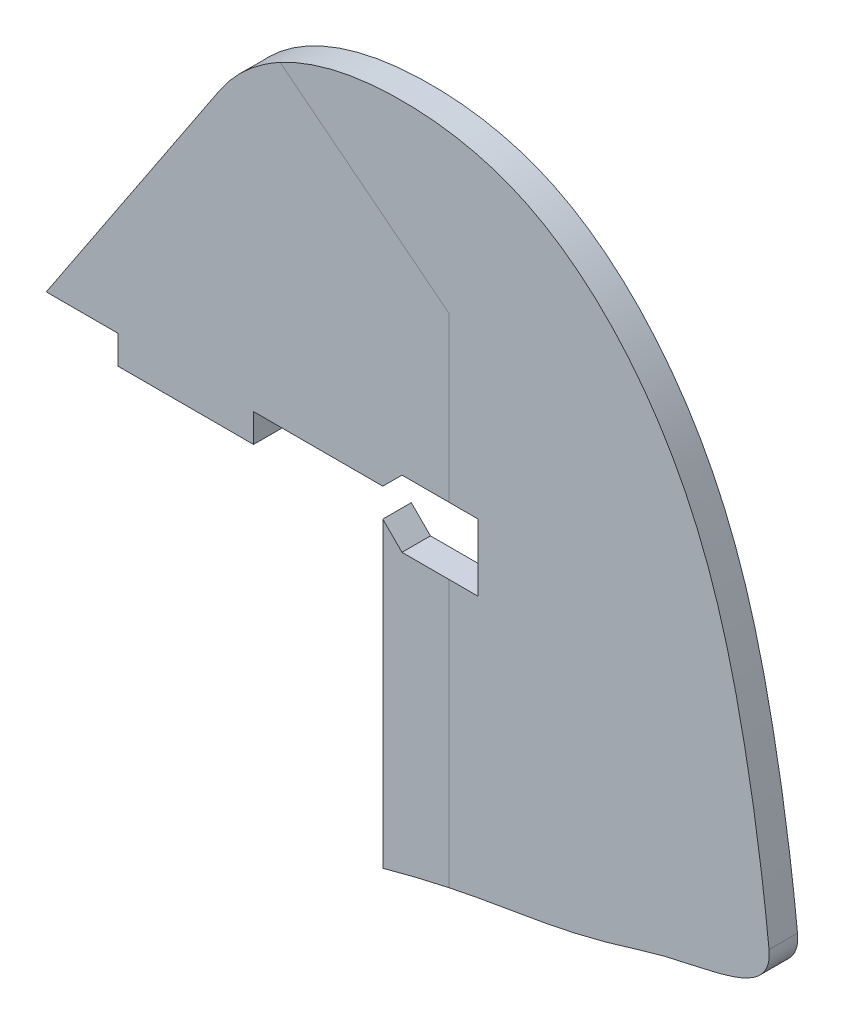
SolidWorks part; units mm, degrees
ref_plane "Front" through (0, 0, 0) normal (0, 0, 1) x (1, 0, 0)
ref_plane "Top" through (0, 0, 0) normal (0, 1, 0) x (1, 0, 0)
ref_plane "Right" through (0, 0, 0) normal (1, 0, 0) x (0, 0, -1)
sketch "Sketch1" plane through (0, 0, 0) normal (0, 0, 1) x (1, 0, 0)
  line L0 (-609.9474, 216.5894) -> (1528.7193, 216.5894) construction
  line L1 (2.6601, 4.007) -> (35.1257, 52.9107)
  line L2 (65.6661, 0) -> (65.6661, 4.007)
  line L3 (65.6661, 4.007) -> (2.6601, 4.007)
  line L4 (65.6661, -57.9378) -> (65.6661, 0)
  line L5 (65.6661, 0) -> (0, 0) construction
  line L6 (78.0167, 38.2576) -> (46.4421, 63.112)
  line L7 (78.0167, 38.2576) -> (78.0167, -55.0278)
  spline S0 degree 3 poles (35.1257, 52.9107) (37.9474, 57.1612) (47.9711, 65.9423) (69.0084, 69.7517) (98.5076, 64.2412) (123.1022, 36.6886) (133.3175, 0.0651) (136.8079, -23.843) (137.976, -34.9736) knots 0 0 0 0 0.083245 0.226859 0.347289 0.588091 0.805835 1 1 1 1
  spline S1 degree 3 poles (137.976, -34.9736) (138.8152, -42.9691) (124.6399, -43.6095) (103.2327, -50.58) (88.628, -52.8063) (74.994, -55.3617) (65.6661, -57.9378) knots 0 0 0 0 0.302584 0.37189 0.693053 1 1 1 1
extrude "Boss-Extrude1" add sketch "Sketch1" along normal mid plane 5.334
split line "Split Line2"
sketch "Sketch1<5>"
sketch "Sketch2" plane through (0, 4.007, 0) normal (0, -1, 0) x (1, 0, 0)
  line L4 (41.4758, -2.667) -> (41.4758, 2.667)
  line L5 (16.0758, -2.667) -> (41.4758, -2.667)
  line L6 (16.0758, 2.667) -> (16.0758, -2.667)
  line L7 (41.4758, 2.667) -> (16.0758, 2.667)
extrude "Elevator Tab" add sketch "Sketch2" along normal blind 5.334
sketch "Sketch3" plane through (0, 0, 2.667) normal (0, 0, 1) x (1, 0, 0)
  line L0 (65.6661, 1.34) -> (132.2592, 1.34) construction
  line L1 (65.6661, -57.9378) -> (65.6661, 4.007) construction
  line L2 (65.6661, 4.007) -> (69.2582, 7.5991)
  line L3 (16.0758, 4.007) -> (2.6601, 4.007) construction
  line L4 (83.4461, -4.9191) -> (83.4461, 7.5991)
  line L5 (83.4461, 7.5991) -> (69.2582, 7.5991)
  line L6 (83.4461, -4.9191) -> (69.2582, -4.9191)
  line L7 (65.6661, -1.327) -> (69.2582, -4.9191)
  line L8 (65.6661, 4.007) -> (65.6661, -1.327)
  spline S0 degree 3 poles (46.4421, 63.112) (53.5235, 66.9463) (69.2544, 69.7058) (98.5076, 64.2412) (123.1022, 36.6886) (133.3175, 0.0651) (136.8079, -23.843) (137.976, -34.9736) knots 0.087454 0.087454 0.087454 0.087454 0.226859 0.347289 0.588091 0.805835 1 1 1 1 construction
  point P16 (83.4461, 1.34)
  dimension "D1" = 45
  dimension "D2" = 5.08
  dimension "D3" = 2.667
  dimension "D4" = 17.78
extrude "Elevator Throw Slot" cut sketch "Sketch3" against normal up to next
sketch "Build Plans" [suppressed] plane through (0, 0, 2.667) normal (0, 0, 1) x (1, 0, 0)
  line L0 (78.0167, -4.9191) -> (69.2582, -4.9191) construction
  line L1 (69.2582, -4.9191) -> (65.6661, -1.327) construction
  line L2 (65.6661, -1.327) -> (65.6661, -57.9378) construction
  line L3 (78.0167, 7.5991) -> (83.4461, 7.5991) construction
  line L4 (83.4461, 7.5991) -> (83.4461, -4.9191) construction
  line L5 (83.4461, -4.9191) -> (78.0167, -4.9191) construction
  line L6 (65.6661, 4.007) -> (69.2582, 7.5991) construction
  line L7 (69.2582, 7.5991) -> (78.0167, 7.5991) construction
  line L8 (35.1257, 52.9107) -> (2.6601, 4.007) construction
  line L9 (2.6601, 4.007) -> (16.0758, 4.007) construction
  line L10 (16.0758, 4.007) -> (16.0758, -1.327) construction
  line L11 (16.0758, -1.327) -> (41.4758, -1.327) construction
  line L12 (41.4758, -1.327) -> (41.4758, 4.007) construction
  line L13 (41.4758, 4.007) -> (65.6661, 4.007) construction
  line L14 (78.0167, -4.9191) -> (69.2582, -4.9191)
  line L15 (69.2582, -4.9191) -> (65.6661, -1.327)
  line L16 (65.6661, -1.327) -> (65.6661, -57.9378)
  line L17 (78.0167, 7.5991) -> (83.4461, 7.5991)
  line L18 (83.4461, 7.5991) -> (83.4461, -4.9191)
  line L19 (83.4461, -4.9191) -> (78.0167, -4.9191)
  line L20 (65.6661, 4.007) -> (69.2582, 7.5991)
  line L21 (69.2582, 7.5991) -> (78.0167, 7.5991)
  line L22 (35.1257, 52.9107) -> (2.6601, 4.007)
  line L23 (2.6601, 4.007) -> (16.0758, 4.007)
  line L24 (16.0758, 4.007) -> (16.0758, -1.327)
  line L25 (16.0758, -1.327) -> (41.4758, -1.327)
  line L26 (41.4758, -1.327) -> (41.4758, 4.007)
  line L27 (41.4758, 4.007) -> (65.6661, 4.007)
  line L28 (78.0167, 38.2576) -> (46.4421, 63.112) construction
  line L29 (78.0167, -54.9114) -> (78.0167, -4.9191) construction
  line L30 (78.0167, 7.5991) -> (78.0167, 38.2576) construction
  line L31 (78.0167, 38.2576) -> (46.4421, 63.112)
  line L32 (78.0167, -54.9114) -> (78.0167, -4.9191)
  line L33 (78.0167, 7.5991) -> (78.0167, 38.2576)
  spline S0 degree 3 poles (-1755.5469, -884.2615) (1700.0402, 725.4267) (-1516.4629, -816.7217) (1915.0572, 734.9656) knots -1.500781 -1.500781 -1.500781 -1.500781 3.824635 3.824635 3.824635 3.824635 only from (65.6661, -57.9378) to (78.0167, -54.9114) construction
  spline S1 degree 3 poles (-1744.1543, -878.9547) (-33.3044, -82.0513) (39.6066, -60.2791) (103.2327, -50.58) (163.2008, -31.0535) (264.2774, -73.6034) (-1498.14, 1114.7439) knots -2.494916 -2.494916 -2.494916 -2.494916 0.152928 0.474092 0.543397 2.09438 2.09438 2.09438 2.09438 only from (78.0167, -54.9114) to (137.976, -34.9736) construction
  spline S2 degree 3 poles (978.4502, 1779.2818) (-46.433, -527.4897) (192.2511, -211.2207) (123.1022, 36.6886) (98.5076, 64.2412) (-7.7749, 84.0951) (-120.2073, -105.0887) (1492.0691, -1305.4806) knots -3.678124 -3.678124 -3.678124 -3.678124 0.281619 0.499363 0.740165 0.860595 2.318271 2.318271 2.318271 2.318271 only from (137.976, -34.9736) to (46.4421, 63.112) construction
  spline S3 degree 3 poles (-1897.8324, 519.2834) (431.9191, -200.4939) (-90.8912, 344.0732) (35.5527, -210.0769) (1496.3301, -1302.0324) knots -1.71486 -1.71486 -1.71486 -1.71486 0.004209 1.282776 1.282776 1.282776 1.282776 only from (46.4421, 63.112) to (35.1257, 52.9107) construction
  spline S4 degree 3 poles (65.6661, -57.9378) (70.3466, -56.6451) (74.3561, -55.6867) (78.0167, -54.9114) knots 0.845982 0.845982 0.845982 0.845982 1 1 1 1
  spline S5 degree 3 poles (78.0167, -54.9114) (81.6515, -54.1416) (91.8533, -52.3147) (103.2327, -50.58) (124.6399, -43.6095) (138.8152, -42.9691) (137.976, -34.9736) knots 0 0 0 0 0.152928 0.474092 0.543397 0.845982 0.845982 0.845982 0.845982
  spline S6 degree 3 poles (137.976, -34.9736) (136.8079, -23.843) (133.3175, 0.0651) (123.1022, 36.6886) (98.5076, 64.2412) (69.2544, 69.7058) (53.5235, 66.9463) (46.4421, 63.112) knots 0.087454 0.087454 0.087454 0.087454 0.281619 0.499363 0.740165 0.860595 1 1 1 1
  spline S7 degree 3 poles (46.4421, 63.112) (46.2283, 62.9963) (41.8116, 60.5463) (37.9474, 57.1612) (35.1257, 52.9107) knots 0 0 0 0 0.004209 0.087454 0.087454 0.087454 0.087454
